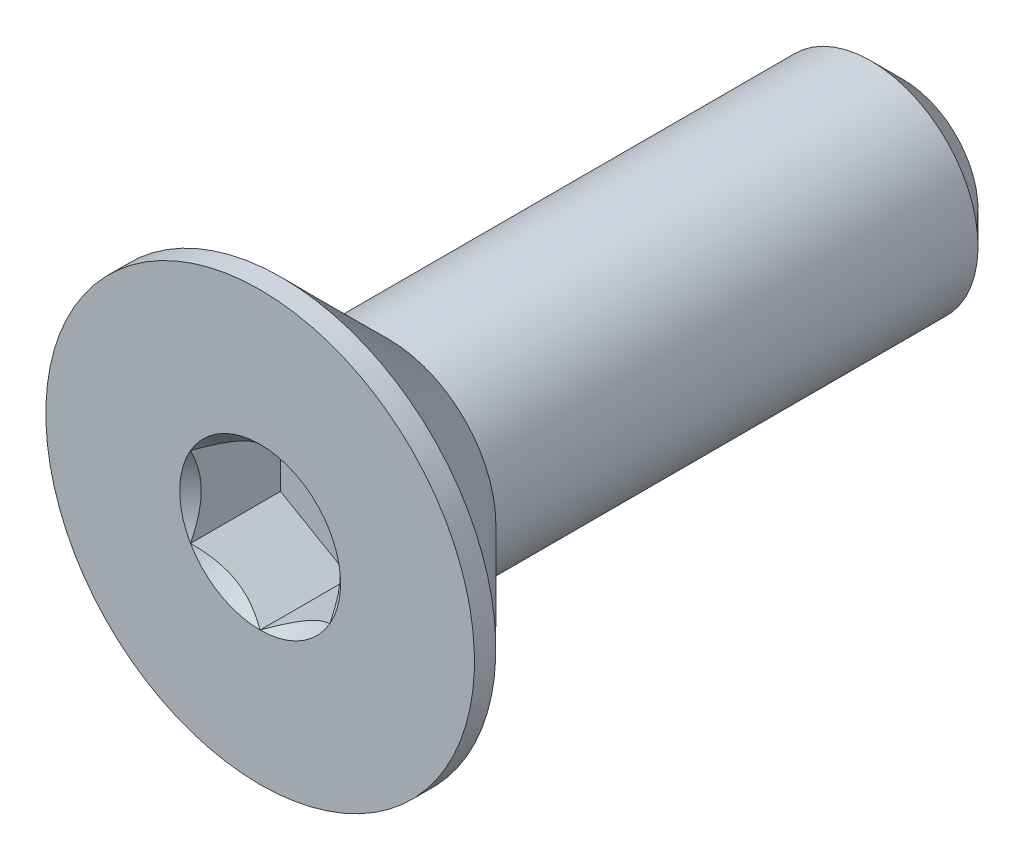
SolidWorks part; units mm, degrees
ref_plane "Front" through (0, 0, 0) normal (0, 0, 1) x (1, 0, 0)
ref_plane "Top" through (0, 0, 0) normal (0, 1, 0) x (1, 0, 0)
ref_plane "Right" through (0, 0, 0) normal (1, 0, 0) x (0, 0, -1)
sketch "Sketch1" plane through (0, 0, 0) normal (1, 0, 0) x (0, 0, -1)
  line L0 (0, 2) -> (0.2, 2) construction
  line L1 (0.2, 2) -> (1.2, 1) construction
  line L2 (0, 1) -> (6, 1)
  line L3 (6, 1) -> (6, 0)
  line L4 (6, 0) -> (0, 0)
  line L5 (0, 0) -> (0, 2) construction
  line L6 (0, 2) -> (0, -2) construction
  line L7 (6, 1) -> (6, -1) construction
  line L8 (0, -2) -> (0.2, -2) construction
  line L9 (0.2, -2) -> (1.2, -1) construction
  line L11 (0, 1) -> (0, 0)
  line L12 (1.2, 1) -> (1.2, 0) construction
  dimension "Head Ht" = 1.2
  dimension "Head Dia" = 4
  dimension "Dia" = 2
  dimension "Lg" = 6
  dimension "Head Angle" = 90
revolve "Revolve1" add sketch "Sketch1" angle 360 mid plane about L4
sketch "Sketch3" plane through (0, 0, -6) normal (0, 0, -1) x (-1, 0, 0)
  circle A0 centre (0, 0) radius 1
curve "Helix/Spiral1" pitch 0.4 height 6 turns 15
sketch "Sketch2" plane through (0, 0, 0) normal (1, 0, 0) x (0, 0, -1)
  line L0 (6, 1) -> (6.35, 1)
  line L1 (6.35, 1) -> (6.2, 0.7402)
  line L2 (6.2, 0.7402) -> (6.15, 0.7402)
  line L3 (6.15, 0.7402) -> (6, 1)
  line L4 (6.075, 0.8701) -> (6.275, 0.8701) construction
  dimension "D1" = 60
  dimension "D2" = 0.05
  dimension "D3" = 0.2
chamfer "Chamfer1" distance 0.3 angle 45 1 edges at (0, 1, -6)
sketch "Sketch7" plane through (0, 0, 0) normal (1, 0, 0) x (0, 0, -1)
  line L0 (0, 2) -> (0.2, 2) construction
  line L1 (0.2, 2) -> (1.2, 1) construction
  line L2 (0, 2) -> (0.2, 2)
  line L3 (0.2, 2) -> (1.2, 1)
  line L4 (1.2, 1) -> (1.2, 0) construction
  line L5 (1.2, 1) -> (1.2, 0)
  line L7 (0, 0) -> (0, 2) construction
  line L8 (0, 0) -> (0, 2)
  line L9 (0, 0) -> (1.2, 0)
  line L10 (2.2, 0) -> (-2.2, 0) construction
revolve "Revolve2" add sketch "Sketch7" angle 360 mid plane about L9
ref_plane "Plane1" through (0, 0, -1.2) normal (0, 0, 1) x (1, 0, 0)
sketch "Sketch8" plane through (0, 0, -1.2) normal (0, 0, 1) x (1, 0, 0)
  circle A0 centre (0, 0) radius 1
extrude "Boss-Extrude1" add sketch "Sketch8" against normal through all draft 45
sketch "Sketch5" plane through (0, 0, 0) normal (0, 0, 1) x (1, 0, 0)
  line L1 (0.65, -0.3753) -> (0.65, 0.3753)
  line L2 (0.65, 0.3753) -> (0, 0.7506)
  line L3 (0, 0.7506) -> (-0.65, 0.3753)
  line L4 (-0.65, 0.3753) -> (-0.65, -0.3753)
  line L5 (-0.65, -0.3753) -> (0, -0.7506)
  line L6 (0, -0.7506) -> (0.65, -0.3753)
  circle A0 centre (0, 0) radius 0.65 construction
  dimension "Hex" = 1.3
extrude "Cut-Extrude2" cut sketch "Sketch5" against normal blind 0.84
sketch "Sketch6" plane through (0, 0, 0) normal (0, 0, 1) x (1, 0, 0)
  circle A0 centre (0, 0) radius 0.7506
extrude "Cut-Extrude3" cut sketch "Sketch6" against normal blind 0.84 draft 45
sketch "Sketch9" [suppressed] plane through (0, 0, -5.5) normal (0, 0, 1) x (1, 0, 0)
  circle A1 centre (0, 0) radius 5
  circle A2 centre (0, 0) radius 5
  point P0 (0, 5)
  dimension "D1" = 0
extrude "Boss-Extrude2" [suppressed] add sketch "Sketch9" against normal offset from surface (18.5 mm away) 26
fillet "Fillet1" [suppressed] radius 0.2
sketch "Sketch10" plane through (0, 0, 0) normal (1, 0, 0) x (0, 0, -1)
  line L0 (6, 1) -> (6, -1) construction
  point P0 (5.4, -1)
  dimension "D1" = 0.6
equation "\"D3@Helix/Spiral1\" = \"Lg@Sketch1\""
equation "\"D2@Sketch2\" = \"D4@Helix/Spiral1\" * .125"
equation "\"D3@Sketch2\" = \"D4@Helix/Spiral1\" * .5"
equation "\"D1@Chamfer1\" = \"D4@Helix/Spiral1\" * .75"
equation "\"D1@Cut-Extrude2\" = \"Head Ht@Sketch1\" * .7"
equation "\"D1@Sketch10\" = \"D4@Helix/Spiral1\" * 1.5"
equation "\"D1@Cut-Extrude3\" = \"D1@Cut-Extrude2\""
equation "\"D1@Fillet1\" = \"Dia@Sketch1\" * .1"
